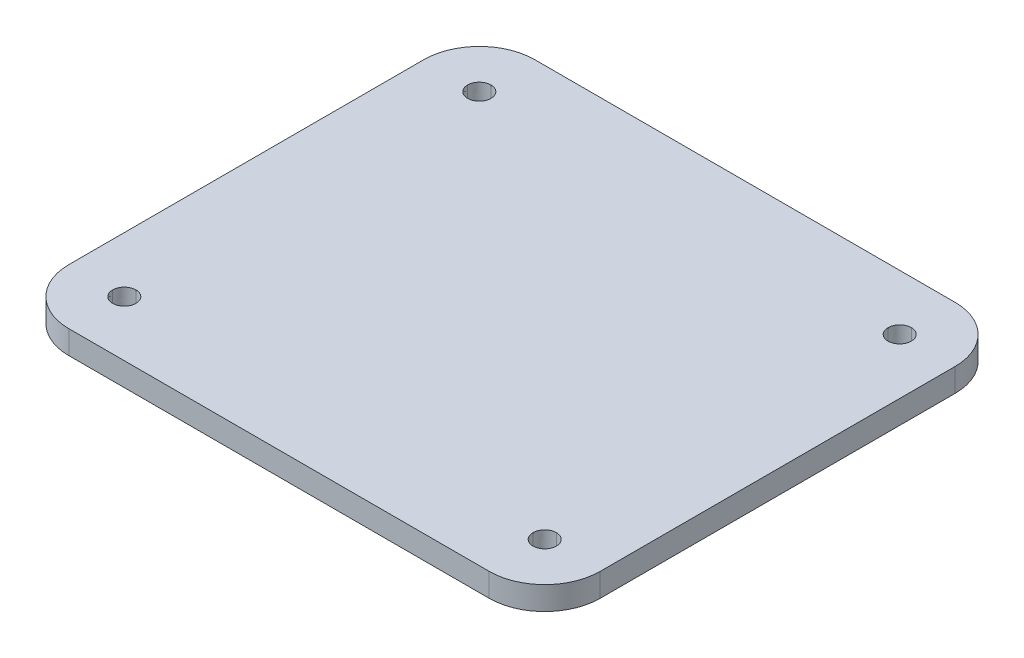
SolidWorks part; units mm, degrees
ref_plane "Front Plane" through (0, 0, 0) normal (0, 0, 1) x (1, 0, 0)
ref_plane "Top Plane" through (0, 0, 0) normal (0, 1, 0) x (1, 0, 0)
ref_plane "Right Plane" through (0, 0, 0) normal (1, 0, 0) x (0, 0, -1)
sketch "Sketch1" plane through (0, 0, 0) normal (0, 1, 0) x (1, 0, 0)
  line L0 (-92.0838, 79.8373) -> (-34.9338, 79.8373) construction
  line L1 (-92.0838, 72.2973) -> (-34.9338, 72.2973)
  line L2 (-99.6238, 79.8373) -> (-99.6238, 128.0973)
  line L3 (-92.0838, 135.6373) -> (-34.9338, 135.6373)
  line L4 (-27.3938, 79.8373) -> (-27.3938, 128.0973)
  line L5 (-34.9338, 79.8373) -> (-34.9338, 128.0973) construction
  line L6 (-34.9338, 128.0973) -> (-92.0838, 128.0973) construction
  line L7 (-92.0838, 128.0973) -> (-92.0838, 79.8373) construction
  circle A0 centre (-34.9338, 79.8373) radius 1.5875
  circle A1 centre (-92.0838, 79.8373) radius 1.5875
  circle A2 centre (-92.0838, 128.0973) radius 1.5875
  circle A3 centre (-34.9338, 128.0973) radius 1.5875
  arc A4 (-34.9338, 72.2973) -> (-27.3938, 79.8373) centre (-34.9338, 79.8373) ccw
  arc A5 (-34.9338, 135.6373) -> (-27.3938, 128.0973) centre (-34.9338, 128.0973) cw
  arc A6 (-99.6238, 128.0973) -> (-92.0838, 135.6373) centre (-92.0838, 128.0973) cw
  arc A7 (-92.0838, 72.2973) -> (-99.6238, 79.8373) centre (-92.0838, 79.8373) cw
  spline S0 degree 3 poles (-33.3463, 79.8373) (-33.3463, 80.7141) (-34.057, 81.4248) (-34.9338, 81.4248) knots 0 0 0 0 0.2 0.2 0.2 0.2
  spline S1 degree 3 poles (-34.9338, 81.4248) (-35.8106, 81.4248) (-36.5213, 80.7141) (-36.5213, 79.8373) knots 0.2 0.2 0.2 0.2 0.4 0.4 0.4 0.4
  spline S2 degree 3 poles (-36.5213, 79.8373) (-36.5213, 78.9605) (-35.8106, 78.2498) (-34.9338, 78.2498) knots 0.4 0.4 0.4 0.4 0.6 0.6 0.6 0.6
  spline S3 degree 3 poles (-34.9338, 78.2498) (-34.057, 78.2498) (-33.3463, 78.9605) (-33.3463, 79.8373) knots 0.6 0.6 0.6 0.6 1 1 1 1
  spline S4 degree 3 poles (-33.3463, 128.0973) (-33.3463, 128.9741) (-34.057, 129.6848) (-34.9338, 129.6848) knots 0 0 0 0 0.2 0.2 0.2 0.2
  spline S5 degree 3 poles (-34.9338, 129.6848) (-35.8106, 129.6848) (-36.5213, 128.9741) (-36.5213, 128.0973) knots 0.2 0.2 0.2 0.2 0.4 0.4 0.4 0.4
  spline S6 degree 3 poles (-36.5213, 128.0973) (-36.5213, 127.2205) (-35.8106, 126.5098) (-34.9338, 126.5098) knots 0.4 0.4 0.4 0.4 0.6 0.6 0.6 0.6
  spline S7 degree 3 poles (-34.9338, 126.5098) (-34.057, 126.5098) (-33.3463, 127.2205) (-33.3463, 128.0973) knots 0.6 0.6 0.6 0.6 1 1 1 1
  spline S8 degree 3 poles (-90.4963, 128.0973) (-90.4963, 128.9741) (-91.207, 129.6848) (-92.0838, 129.6848) knots 0 0 0 0 0.2 0.2 0.2 0.2
  spline S9 degree 3 poles (-92.0838, 129.6848) (-92.9606, 129.6848) (-93.6713, 128.9741) (-93.6713, 128.0973) knots 0.2 0.2 0.2 0.2 0.4 0.4 0.4 0.4
  spline S10 degree 3 poles (-93.6713, 128.0973) (-93.6713, 127.2205) (-92.9606, 126.5098) (-92.0838, 126.5098) knots 0.4 0.4 0.4 0.4 0.6 0.6 0.6 0.6
  spline S11 degree 3 poles (-92.0838, 126.5098) (-91.207, 126.5098) (-90.4963, 127.2205) (-90.4963, 128.0973) knots 0.6 0.6 0.6 0.6 1 1 1 1
  spline S12 degree 3 poles (-90.4963, 79.8373) (-90.4963, 80.7141) (-91.207, 81.4248) (-92.0838, 81.4248) knots 0 0 0 0 0.2 0.2 0.2 0.2
  spline S13 degree 3 poles (-92.0838, 81.4248) (-92.9606, 81.4248) (-93.6713, 80.7141) (-93.6713, 79.8373) knots 0.2 0.2 0.2 0.2 0.4 0.4 0.4 0.4
  spline S14 degree 3 poles (-93.6713, 79.8373) (-93.6713, 78.9605) (-92.9606, 78.2498) (-92.0838, 78.2498) knots 0.4 0.4 0.4 0.4 0.6 0.6 0.6 0.6
  spline S15 degree 3 poles (-92.0838, 78.2498) (-91.207, 78.2498) (-90.4963, 78.9605) (-90.4963, 79.8373) knots 0.6 0.6 0.6 0.6 1 1 1 1
  dimension "D3" = 7.54
  dimension "D4" = 7.54
  dimension "D5" = 7.54
  dimension "D6" = 7.54
  dimension "D7" = 72.23
  dimension "D8" = 63.34
  dimension "D11" = 3.175
  dimension "D2" = 7.54
extrude "Boss-Extrude1" add sketch "Sketch1" along normal blind 3.175
